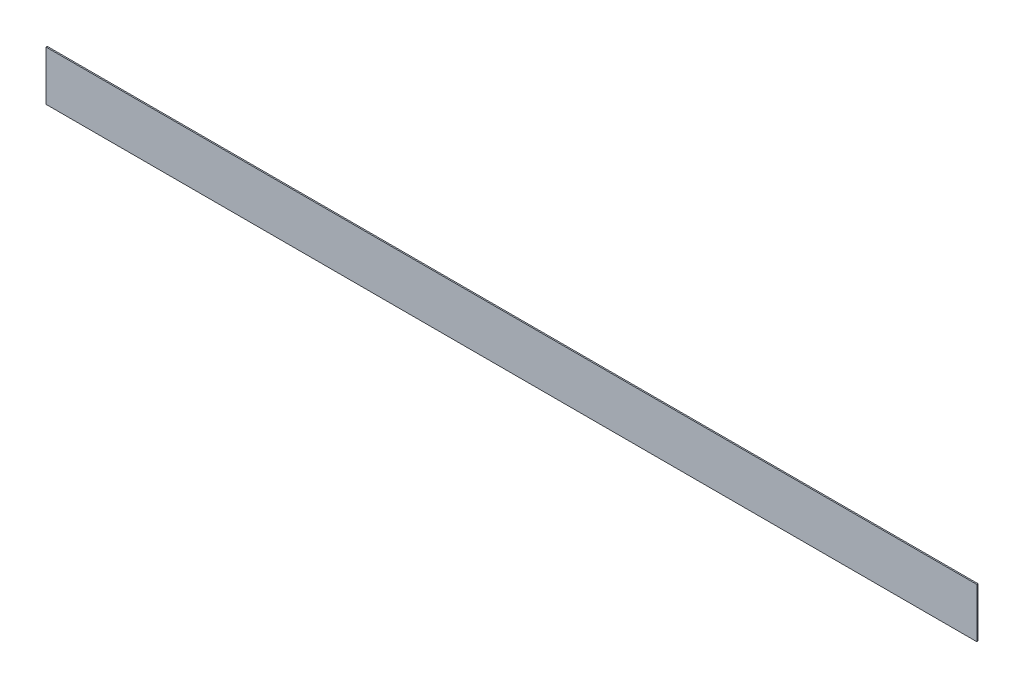
SolidWorks part; units mm, degrees
ref_plane "Front Plane" through (0, 0, 0) normal (0, 0, 1) x (1, 0, 0)
ref_plane "Top Plane" through (0, 0, 0) normal (0, 1, 0) x (1, 0, 0)
ref_plane "Right Plane" through (0, 0, 0) normal (1, 0, 0) x (0, 0, -1)
sketch "Sketch1" plane through (0, 0, 0) normal (0, 0, 1) x (1, 0, 0)
  line L5 (0, 0) -> (75, 0)
  line L6 (0, 0) -> (0, -4)
  line L7 (0, -4) -> (75, -4)
  line L8 (75, 0) -> (75, -4)
  dimension "D1" = 4
  dimension "D2" = 75
extrude "Boss-Extrude1" add sketch "Sketch1" along normal blind 0.1
